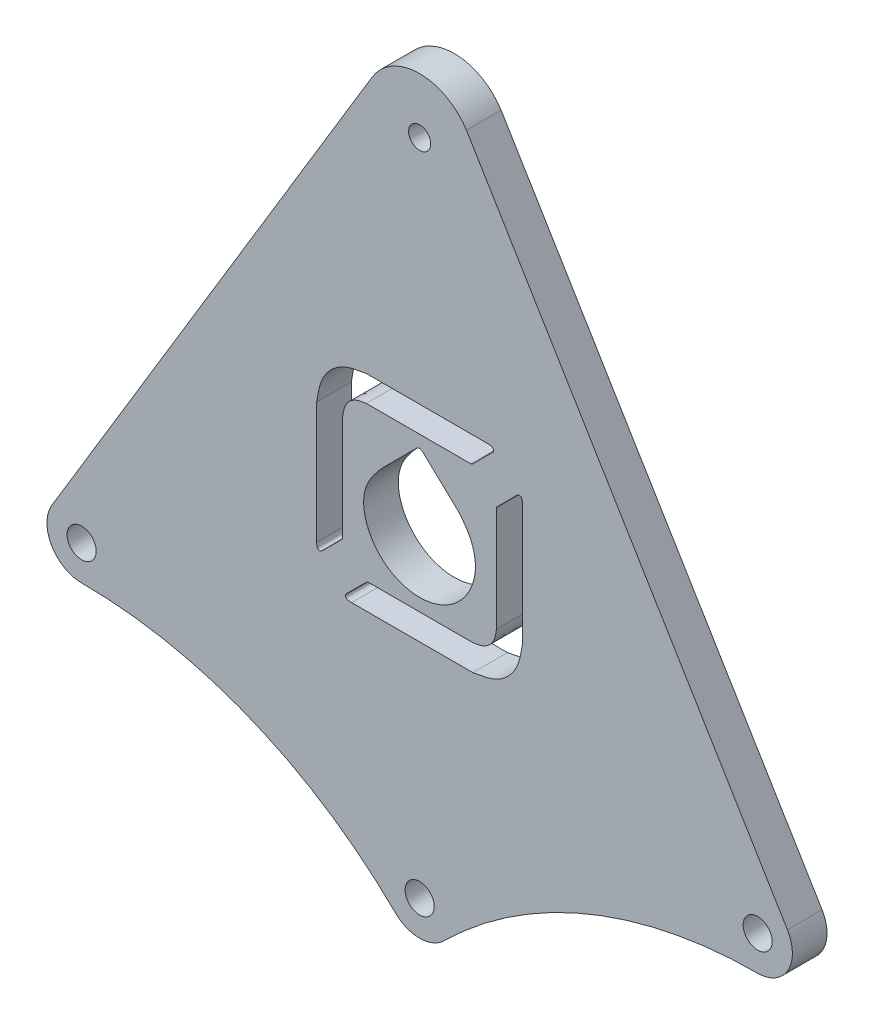
SolidWorks part; units mm, degrees
ref_plane "Front Plane" through (0, 0, 0) normal (0, 0, 1) x (1, 0, 0)
ref_plane "Top Plane" through (0, 0, 0) normal (0, 1, 0) x (1, 0, 0)
ref_plane "Right Plane" through (0, 0, 0) normal (1, 0, 0) x (0, 0, -1)
sketch "Sketch1" plane through (0, 0, 0) normal (0, 0, 1) x (1, 0, 0)
  line L0 (-48.75, 20) -> (48.75, 20) construction
  line L1 (0, 20) -> (0, 0) construction
  line L2 (0, 0) -> (0, -5) construction
  line L3 (-6.85, 99.1325) -> (-53.0312, 22.5828)
  line L4 (6.7459, 99.3003) -> (53.0312, 22.5829)
  circle A0 centre (0, 0) radius 2.1
  arc A1 (3.5115, -3.5594) -> (48.75, 15) centre (48.75, -49.4141) cw
  circle A2 centre (-48.75, 20) radius 2.1
  arc A3 (53.0312, 22.5829) -> (48.75, 15) centre (48.75, 20) cw
  arc A4 (-53.0312, 22.5828) -> (-48.75, 15) centre (-48.75, 20) ccw
  arc A5 (-3.5115, -3.5594) -> (3.5115, -3.5594) centre (0, 0) ccw
  arc A6 (-3.5115, -3.5594) -> (-48.75, 15) centre (-48.75, -49.4141) ccw
  circle A8 centre (48.75, 20) radius 2.1
  circle A9 centre (0, 95) radius 1.6
  arc A10 (6.7459, 99.3003) -> (-6.85, 99.1325) centre (0, 95) ccw
  dimension "D1" = 4.2
  dimension "D2" = 48.75
  dimension "D3" = 8
  dimension "D4" = 10
  dimension "D5" = 3.2
  dimension "D6" = 95
extrude "Boss-Extrude1" add sketch "Sketch1" along normal blind 5
sketch "Sketch2" plane through (0, 0, 5) normal (0, 0, 1) x (1, 0, 0)
  line L0 (0, 95) -> (0, 0) construction
  line L7 (-0.4439, 55.9843) -> (-5.2973, 51.1312)
  line L8 (5.5576, 51.1312) -> (0.4078, 55.9843)
  line L9 (-7.7061, 57.9511) -> (7.3726, 57.9511)
  line L10 (7.6331, 58.0611) -> (10.56, 60.9881)
  line L11 (9.7814, 61.6923) -> (-7.7061, 61.6923)
  line L12 (-14.8551, 54.5428) -> (-14.8537, 37.0557)
  line L13 (-14.1495, 36.2786) -> (-11.2239, 39.2055)
  line L14 (-11.1124, 39.4645) -> (-11.1139, 54.5428)
  line L15 (7.67, 35.756) -> (-7.4083, 35.756)
  line L16 (-7.6688, 35.6445) -> (-10.5957, 32.7176)
  line L17 (-9.8171, 32.0134) -> (7.67, 32.0134)
  line L18 (14.8194, 39.1642) -> (14.818, 56.65)
  line L19 (14.1138, 57.4272) -> (11.1869, 54.5002)
  line L20 (11.0768, 54.2413) -> (11.0779, 39.1642)
  spline S0 degree 3 poles (0, 56.1692) (-0.0526, 56.1641) (-0.161, 56.1536) (-0.3153, 56.0898) (-0.4012, 56.0193) (-0.4439, 55.9843) knots 0 0 0 0 0.322338 0.663828 1 1 1 1
  spline S1 degree 3 poles (-5.2973, 51.1312) (-5.3018, 51.127) (-5.3105, 51.1188) (-5.3229, 51.1064) (-5.7814, 50.6001) (-6.6748, 49.5547) (-7.775, 47.7503) (-8.3328, 44.9274) (-7.2905, 41.3921) (-4.2229, 38.3301) (-0.003, 37.1867) (4.214, 38.3278) (7.269, 41.3961) (8.2776, 44.9166) (7.7671, 47.7117) (6.8532, 49.5853) (5.9795, 50.6278) (5.5576, 51.1312) knots 0 0 0 0 0.000489 0.000958 0.001407 0.055155 0.111027 0.168427 0.280644 0.38981 0.50219 0.614354 0.723171 0.835316 0.891384 0.947546 1 1 1 1
  spline S2 degree 3 poles (0.4078, 55.9843) (0.3686, 56.0182) (0.2913, 56.0852) (0.1516, 56.1544) (0.0505, 56.1642) (0, 56.1692) knots 0 0 0 0 0.338885 0.669777 1 1 1 1
  spline S3 degree 3 poles (7.3726, 57.9511) (7.3948, 57.9527) (7.4381, 57.956) (7.5033, 57.9637) (7.5525, 57.9897) (7.5885, 58.0152) (7.6118, 58.0386) (7.6261, 58.0537) (7.6331, 58.0611) knots 0 0 0 0 0.227493 0.445972 0.663373 0.787115 0.896006 1 1 1 1
  spline S4 degree 3 poles (10.56, 60.9881) (10.589, 61.0274) (10.647, 61.1061) (10.671, 61.2543) (10.6438, 61.3902) (10.5765, 61.4997) (10.486, 61.5786) (10.353, 61.628) (10.1929, 61.6603) (10.0078, 61.6936) (9.8775, 61.691) (9.8061, 61.6926) (9.7938, 61.6932) (9.7855, 61.6926) (9.7814, 61.6923) knots 0 0 0 0 0.104345 0.208931 0.313565 0.397995 0.482811 0.567894 0.701187 0.836715 0.973247 0.982163 0.991064 1 1 1 1
  spline S5 degree 3 poles (-7.7061, 61.6923) (-8.955, 61.4928) (-11.421, 61.0988) (-14.2616, 58.2583) (-14.6555, 55.792) (-14.8551, 54.5428) knots 0 0 0 0 0.336154 0.663772 1 1 1 1
  spline S6 degree 3 poles (-14.8537, 37.0557) (-14.854, 37.0517) (-14.8546, 37.0438) (-14.8539, 37.0319) (-14.8524, 36.9607) (-14.8554, 36.8302) (-14.8216, 36.6447) (-14.7918, 36.4838) (-14.7403, 36.3517) (-14.6616, 36.2614) (-14.5525, 36.1934) (-14.4162, 36.1662) (-14.2677, 36.1905) (-14.1889, 36.2492) (-14.1495, 36.2786) knots 0 0 0 0 0.008622 0.017031 0.025643 0.162638 0.298245 0.431901 0.516392 0.601007 0.685957 0.790142 0.895037 1 1 1 1
  spline S7 degree 3 poles (-11.2239, 39.2055) (-11.215, 39.2148) (-11.1974, 39.233) (-11.1702, 39.26) (-11.1415, 39.2955) (-11.1216, 39.3446) (-11.112, 39.4039) (-11.1123, 39.4437) (-11.1124, 39.4645) knots 0 0 0 0 0.131285 0.25763 0.390972 0.594165 0.788898 1 1 1 1
  spline S8 degree 3 poles (-11.1139, 54.5428) (-11.0256, 55.1467) (-10.8532, 56.3271) (-9.4912, 57.6901) (-8.3104, 57.8627) (-7.7061, 57.9511) knots 0 0 0 0 0.33841 0.661392 1 1 1 1
  spline S9 degree 3 poles (-7.4083, 35.756) (-7.4274, 35.7553) (-7.4626, 35.754) (-7.5166, 35.7455) (-7.5609, 35.7252) (-7.6008, 35.7014) (-7.6353, 35.6754) (-7.6573, 35.6551) (-7.6688, 35.6445) knots 0 0 0 0 0.196746 0.361608 0.557262 0.692766 0.839563 1 1 1 1
  spline S10 degree 3 poles (-10.5957, 32.7176) (-10.6247, 32.6783) (-10.6827, 32.5996) (-10.7067, 32.4514) (-10.6795, 32.3155) (-10.6119, 32.206) (-10.5215, 32.1274) (-10.389, 32.0774) (-10.2289, 32.0449) (-10.0439, 32.0146) (-9.9133, 32.0091) (-9.842, 32.0143) (-9.8295, 32.0137) (-9.8212, 32.0135) (-9.8171, 32.0134) knots 0 0 0 0 0.104385 0.20895 0.313569 0.398093 0.483012 0.567612 0.700915 0.836485 0.973043 0.982112 0.991066 1 1 1 1
  spline S11 degree 3 poles (7.67, 32.0134) (8.919, 32.2131) (11.3854, 32.6073) (14.2265, 35.4481) (14.6201, 37.9149) (14.8194, 39.1642) knots 0 0 0 0 0.336157 0.663806 1 1 1 1
  spline S12 degree 3 poles (14.818, 56.65) (14.8183, 56.6541) (14.8189, 56.6624) (14.8182, 56.6749) (14.8167, 56.7463) (14.8193, 56.8767) (14.7859, 57.0618) (14.7541, 57.2218) (14.7041, 57.3543) (14.6255, 57.4448) (14.516, 57.5124) (14.38, 57.5396) (14.2316, 57.5152) (14.1531, 57.4565) (14.1138, 57.4272) knots 0 0 0 0 0.008953 0.017947 0.027021 0.163491 0.298949 0.432165 0.516776 0.601601 0.686035 0.790672 0.895263 1 1 1 1
  spline S13 degree 3 poles (11.1869, 54.5002) (11.1773, 54.491) (11.1584, 54.4729) (11.1298, 54.4451) (11.0994, 54.4118) (11.0826, 54.3624) (11.078, 54.3038) (11.0772, 54.263) (11.0768, 54.2413) knots 0 0 0 0 0.134582 0.264928 0.404991 0.586048 0.77989 1 1 1 1
  spline S14 degree 3 poles (11.0779, 39.1642) (10.99, 38.5601) (10.8181, 37.3795) (9.4553, 36.0168) (8.2744, 35.8443) (7.67, 35.756) knots 0 0 0 0 0.338406 0.661372 1 1 1 1
extrude "Cut-Extrude1" cut sketch "Sketch2" against normal through all
